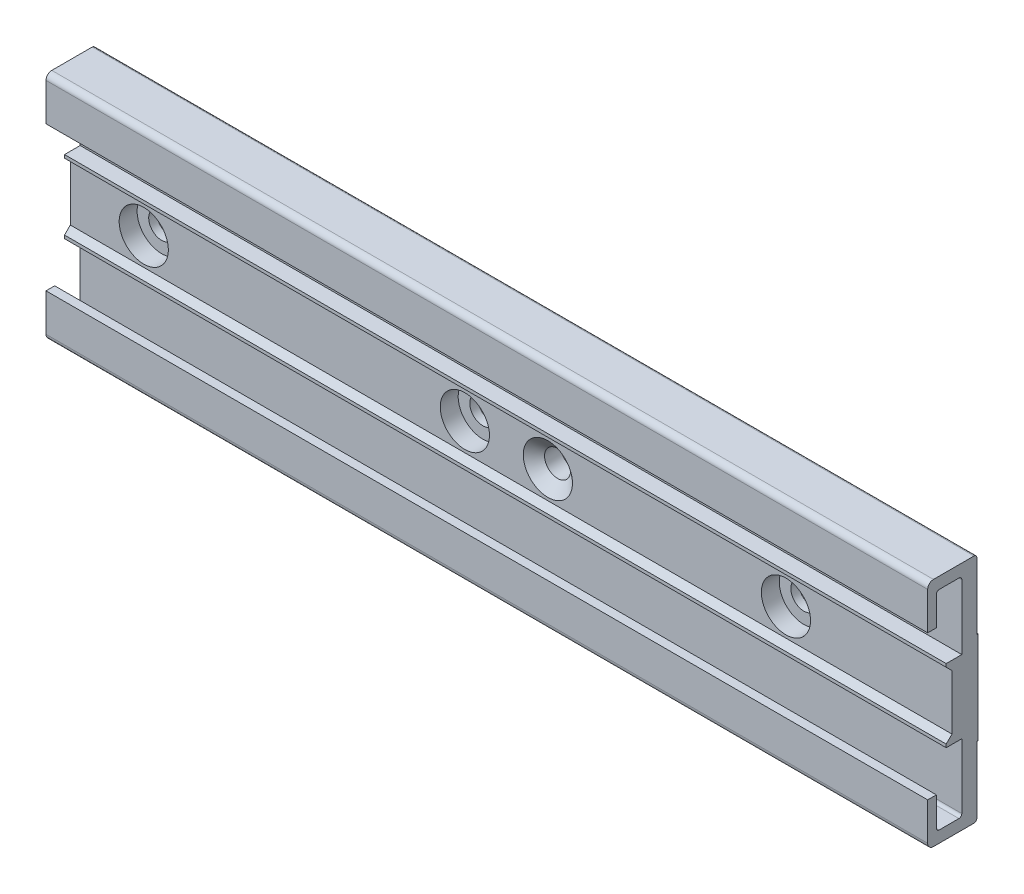
SolidWorks part; units mm, degrees
material "6061-T6 (SS)"
ref_plane "Front Plane" through (0, 0, 0) normal (0, 0, 1) x (1, 0, 0)
ref_plane "Top Plane" through (0, 0, 0) normal (0, 1, 0) x (1, 0, 0)
ref_plane "Right Plane" through (0, 0, 0) normal (1, 0, 0) x (0, 0, -1)
sketch "Sketch1" plane through (0, 0, 0) normal (1, 0, 0) x (0, 0, -1)
  line L0 (-8.7, -12.5) -> (-8.7, -19)
  line L1 (-7.7, -20) -> (-0.7, -20)
  line L2 (-0.2, -19.5) -> (-0.2, -8)
  line L3 (-0.2, -8) -> (0, -8)
  line L4 (0, -8) -> (0, 8)
  line L5 (0, 8) -> (-0.2, 8)
  line L6 (-0.2, 8) -> (-0.2, 19.5)
  line L7 (-0.7, 20) -> (-7.7, 20)
  line L8 (-8.7, 19) -> (-8.7, 12.5)
  line L9 (-8.7, 12.5) -> (-7.2, 12.5)
  line L10 (-7.2, 12.5) -> (-7.2, 17.5)
  line L11 (-6.7, 18) -> (-3.3, 18)
  line L12 (-2.8, 17.5) -> (-2.8, 6.3)
  line L13 (-2.8, 6.3) -> (-5.5, 6.3)
  line L14 (-5.5, 6.3) -> (-5.5, 5.75)
  line L15 (-5.5, 5.75) -> (-4.5, 4.75)
  line L16 (-4.5, 4.75) -> (-4.5, -4.75)
  line L17 (-4.5, -4.75) -> (-5.5, -5.75)
  line L18 (-5.5, -5.75) -> (-5.5, -6.3)
  line L19 (-5.5, -6.3) -> (-2.8, -6.3)
  line L20 (-2.8, -6.3) -> (-2.8, -17.5)
  line L21 (-3.3, -18) -> (-6.7, -18)
  line L22 (-7.2, -17.5) -> (-7.2, -12.5)
  line L23 (-7.2, -12.5) -> (-8.7, -12.5)
  arc A0 (-8.7, -19) -> (-7.7, -20) centre (-7.7, -19) ccw
  arc A1 (-0.7, -20) -> (-0.2, -19.5) centre (-0.7, -19.5) ccw
  arc A2 (-0.2, 19.5) -> (-0.7, 20) centre (-0.7, 19.5) ccw
  arc A3 (-7.7, 20) -> (-8.7, 19) centre (-7.7, 19) ccw
  arc A4 (-6.7, 18) -> (-7.2, 17.5) centre (-6.7, 17.5) ccw
  arc A5 (-2.8, 17.5) -> (-3.3, 18) centre (-3.3, 17.5) ccw
  arc A6 (-3.3, -18) -> (-2.8, -17.5) centre (-3.3, -17.5) ccw
  arc A7 (-7.2, -17.5) -> (-6.7, -18) centre (-6.7, -17.5) ccw
  point P40 (0, 0)
extrude "Boss-Extrude1" add sketch "Sketch1" along normal blind 152.4
hole_wizard "CBORE for #0 Binding Head Machine Screw1" positions "Sketch4" profile "Sketch5" counterbore size "#0" standard "ANSI Inch" end condition through all
sketch "Sketch4" plane through (0, 0, 4.5) normal (0, 0, 1) x (1, 0, 0)
  line L0 (0, 17.5) -> (0, 6.3) construction
  point P0 (12.7, 0)
  point P12 (68.2, 0)
  point P13 (123.7, 0)
  point P14 (179.2, 0)
  point P15 (234.7, 0)
  point P16 (290.2, 0)
  point P17 (345.7, 0)
  dimension "D1" = 12.7
  dimension "D3" = 55.5
  dimension "D2" = 7
sketch "Sketch5" plane through (12.7, 0, 4.5) normal (1, 0, 0) x (0, -1, 0)
  line L0 (0, 0) -> (0, 4.5)
  line L1 (0, 4.5) -> (2.25, 4.5)
  line L3 (2.25, 4.5) -> (2.25, 3.1)
  line L4 (2.25, 3.1) -> (4.25, 3.1)
  line L5 (4.25, 3.1) -> (4.25, 0)
  line L7 (4.25, 0) -> (0, 0)
  line L11 (0, -6.35) -> (0, 107.95) construction
  dimension "Thru Hole Dia." = 4.5
  dimension "Thru Hole Depth" = 4.5
  dimension "C'Bore Dia." = 8.5
  dimension "C'Bore Depth" = 3.1
hole_wizard "CSK for #0 Flat Head Machine Screw (100)1" positions "Sketch6" profile "Sketch7" countersink size "#0" standard "ANSI Inch" end condition through all
sketch "Sketch6" plane through (0, 0, 4.5) normal (0, 0, 1) x (1, 0, 0)
  line L0 (12.7, 0) -> (82.55, 0) construction
  point P0 (82.55, 0)
  dimension "D1" = 69.85
sketch "Sketch7" plane through (82.55, 0, 4.5) normal (1, 0, 0) x (0, -1, 0)
  line L0 (0, 0) -> (0, 4.5)
  line L1 (0, 4.5) -> (2.25, 4.5)
  line L2 (2.25, 4.5) -> (2.25, 1.6782)
  line L3 (2.25, 1.6782) -> (4.25, 0)
  line L5 (4.25, 0) -> (0, 0)
  line L6 (-2.25, 1.6782) -> (-4.25, 0) construction
  line L11 (0, -6.35) -> (0, 107.95) construction
  dimension "Thru Hole Dia." = 4.5
  dimension "Thru Hole Depth" = 4.5
  dimension "Near C'Sink Dia." = 8.5
  dimension "Near C'Sink Angle" = 100
